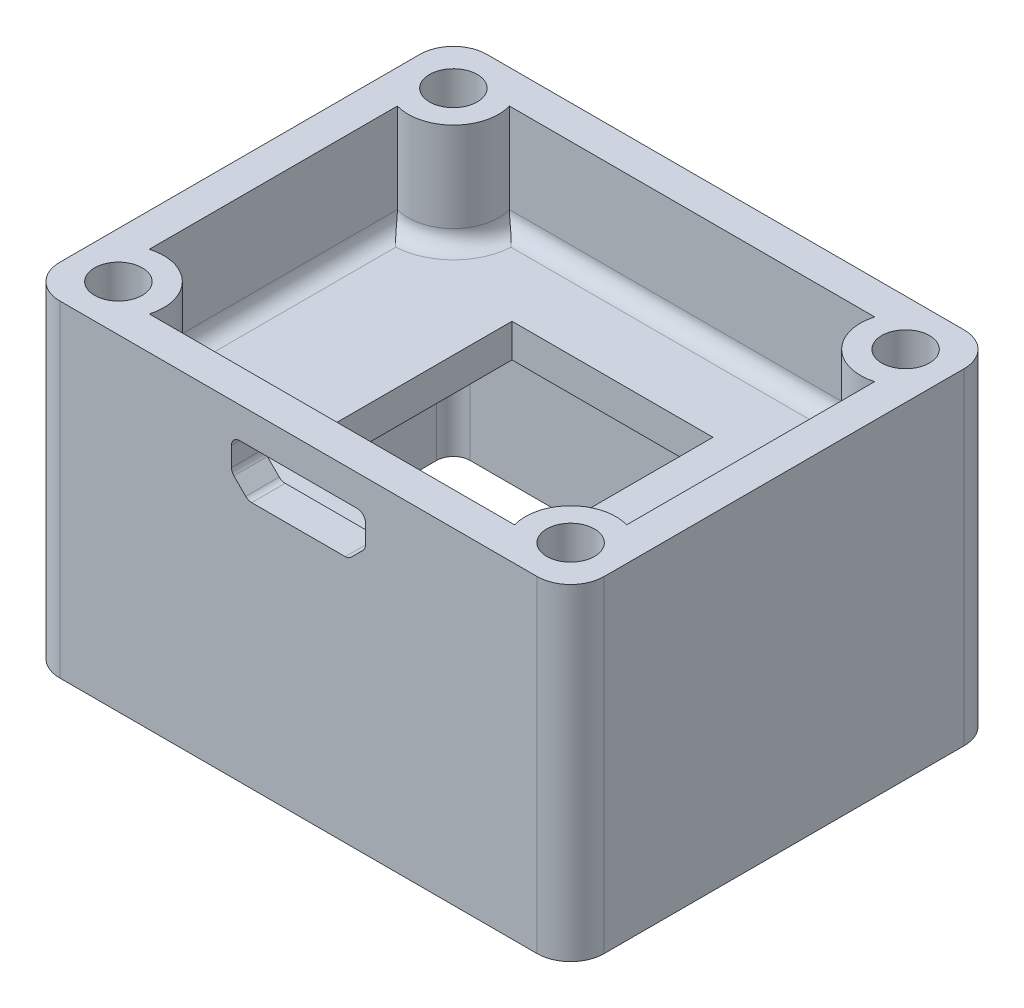
SolidWorks part; units mm, degrees
material "ABS"
ref_plane "Front" through (0, 0, 0) normal (0, 0, 1) x (1, 0, 0)
ref_plane "Top" through (0, 0, 0) normal (0, 1, 0) x (1, 0, 0)
ref_plane "Right" through (0, 0, 0) normal (1, 0, 0) x (0, 0, -1)
sketch "草图1" plane through (0, 0, 0) normal (0, 1, 0) x (1, 0, 0)
  line L0 (-14.25, 10.75) -> (-16.25, 10.75) construction
  line L5 (-14.25, 10.75) -> (14.25, 10.75)
  line L6 (-14.25, 10.75) -> (-14.25, -10.75)
  line L11 (-14.25, -10.75) -> (14.25, -10.75)
  line L12 (14.25, 10.75) -> (14.25, -10.75)
  line L13 (-14.25, 10.75) -> (14.25, -10.75) construction
  line L14 (-14.25, -10.75) -> (14.25, 10.75) construction
  line L15 (-16.25, 12.75) -> (16.25, 12.75)
  line L16 (-16.25, 12.75) -> (-16.25, -12.75)
  line L17 (-16.25, -12.75) -> (16.25, -12.75)
  line L18 (16.25, 12.75) -> (16.25, -12.75)
  line L19 (-16.25, 12.75) -> (16.25, -12.75) construction
  line L20 (-16.25, -12.75) -> (16.25, 12.75) construction
  line L21 (-14.25, 10.75) -> (-14.25, 12.75) construction
  point P0 (0, 0)
  point P6 (0, 0)
  dimension "D3" = 28.5
  dimension "D2" = 2
  dimension "D4" = 21.5
extrude "凸台-拉伸1" add sketch "草图1" along normal blind 13.2
sketch "草图2" plane through (0, 13.2, 0) normal (0, 1, 0) x (1, 0, 0)
  line L1 (-14.25, 10.75) -> (14.25, 10.75)
  line L2 (-14.25, 10.75) -> (-14.25, -10.75)
  line L3 (-14.25, -10.75) -> (14.25, -10.75)
  line L4 (14.25, 10.75) -> (14.25, -10.75)
  line L5 (-14.25, 10.75) -> (14.25, -10.75) construction
  line L6 (-14.25, -10.75) -> (14.25, 10.75) construction
  line L7 (-6, 6) -> (6, 6)
  line L8 (-6, 6) -> (-6, -6)
  line L9 (-6, -6) -> (6, -6)
  line L10 (6, 6) -> (6, -6)
  line L11 (-6, 6) -> (6, -6) construction
  line L12 (-6, -6) -> (6, 6) construction
  point P0 (0, 0)
  point P7 (0, 0)
  point P8 (0, 0)
  dimension "D1" = 12
extrude "凸台-拉伸2" add sketch "草图2" against normal blind 2
sketch "草图3" plane through (0, 13.2, 0) normal (0, 1, 0) x (1, 0, 0)
  line L0 (0, 0) -> (-16.25, 0) construction
  line L1 (-16.25, 12.75) -> (-16.25, -12.75) construction
  line L2 (-16.25, -12.75) -> (-16.25, 12.75)
  line L3 (-16.25, 12.75) -> (16.25, 12.75)
  line L4 (16.25, 12.75) -> (16.25, -0.0404)
  line L5 (16.25, -12.75) -> (16.25, 12.75) construction
  line L7 (14.25, 0.0137) -> (14.25, 10.75)
  line L8 (14.25, 10.75) -> (-14.25, 10.75)
  line L9 (-14.25, 10.75) -> (-14.25, -10.75)
  line L10 (14.25, -10.75) -> (-14.25, -10.75)
  line L11 (14.25, 0.0137) -> (14.25, -10.75)
  line L13 (16.25, -12.75) -> (16.25, -0.0404)
  line L14 (-16.25, -12.75) -> (16.25, -12.75)
  line L15 (14.25, 10.75) -> (-14.25, 10.75) construction
  line L16 (-14.25, 10.75) -> (-14.25, -10.75) construction
  line L17 (14.25, -10.75) -> (14.25, 10.75) construction
  point P17 (-14.25, 0)
extrude "凸台-拉伸3" add sketch "草图3" along normal blind 6.3
sketch "草图6" plane through (0, 19.5, 0) normal (0, 1, 0) x (1, 0, 0)
  line L0 (16.25, 0) -> (0, 0) construction
  line L2 (0, 0) -> (0, 12.75) construction
  line L4 (16.25, -12.75) -> (16.25, 12.75) construction
  line L5 (16.25, 12.75) -> (-16.25, 12.75) construction
  circle A0 centre (13.5, 10) radius 2.7
  circle A1 centre (13.5, -10) radius 2.7
  circle A2 centre (-13.5, -10) radius 2.7
  circle A3 centre (-13.5, 10) radius 2.7
  dimension "D1" = 5.4
  dimension "D2" = 27
  dimension "D3" = 20
extrude "凸台-拉伸4" add sketch "草图6" against normal up to next
sketch "草图7" plane through (0, 19.5, 0) normal (0, 1, 0) x (1, 0, 0)
  line L0 (0, 12.75) -> (0, 0) construction
  line L2 (0, 0) -> (16.25, 0) construction
  line L4 (16.25, 12.75) -> (-16.25, 12.75) construction
  line L5 (16.25, -12.75) -> (16.25, 12.75) construction
  circle A0 centre (13.5, 10) radius 1.425
  circle A1 centre (13.5, -10) radius 1.425
  circle A2 centre (-13.5, -10) radius 1.425
  circle A3 centre (-13.5, 10) radius 1.425
  dimension "D1" = 2.85
extrude "切除-拉伸3" cut sketch "草图7" against normal blind 5.5
sketch "草图10" plane through (0, 11.2, 0) normal (0, -1, 0) x (1, 0, 0)
  line L1 (-7.1, 7.1) -> (7.1, 7.1)
  line L2 (-7.1, 7.1) -> (-7.1, -7.1)
  line L3 (-7.1, -7.1) -> (7.1, -7.1)
  line L4 (7.1, 7.1) -> (7.1, -7.1)
  line L5 (-7.1, 7.1) -> (7.1, -7.1) construction
  line L6 (-7.1, -7.1) -> (7.1, 7.1) construction
  line L7 (-7.9, 7.9) -> (7.9, 7.9)
  line L8 (-7.9, 7.9) -> (-7.9, -7.9)
  line L9 (-7.9, -7.9) -> (7.9, -7.9)
  line L10 (7.9, 7.9) -> (7.9, -7.9)
  line L11 (-7.9, 7.9) -> (7.9, -7.9) construction
  line L12 (-7.9, -7.9) -> (7.9, 7.9) construction
  point P11 (0, 0)
  point P13 (0, 0)
  dimension "D1" = 14.2
  dimension "D2" = 0.8
extrude "凸台-拉伸5" add sketch "草图10" along normal blind 0.8 contours L10 L7 L8 L9 L1 L4 L3 L2
sketch "草图11" plane through (0, 0, 12.75) normal (0, 0, 1) x (1, 0, 0)
  line L0 (0, 0) -> (0, 19.5) construction
  line L1 (-4, 17.65) -> (4, 17.65)
  line L2 (4, 17.65) -> (4, 15.8)
  line L3 (4, 15.8) -> (3, 14.8)
  line L4 (3, 14.8) -> (-3, 14.8)
  line L5 (-4, 15.8) -> (-3, 14.8)
  line L6 (-4, 17.65) -> (-4, 15.8)
  line L7 (-16.25, 19.5) -> (16.25, 19.5) construction
  line L8 (-10.9063, 13.2) -> (10.9063, 13.2) construction
  point P7 (0, 14.8)
  point P9 (0, 17.65)
  dimension "D1" = 8
  dimension "D2" = 135
  dimension "D3" = 1
  dimension "D4" = 1.6
  dimension "D5" = 2.85
extrude "切除-拉伸5" cut sketch "草图11" against normal blind 3
fillet "圆角6" radius 0.5 6 edges at (4, 15.8, 11.75) (3, 14.8, 11.75) (-3, 14.8, 11.75) (-4, 15.8, 11.75) (-4, 17.65, 11.75) (4, 17.65, 11.75)
fillet "圆角3" radius 0.95 8 edges at (0, 13.2, -10.75) (11.5908, 13.2, -8.0908) (11.5908, 13.2, 8.0908) (0, 13.2, 10.75) (-11.5908, 13.2, 8.0908) (-14.25, 13.2, 0) (-11.5908, 13.2, -8.0908) (14.25, 13.2, 0)
fillet "圆角1" radius 2 4 edges at (16.25, 9.75, -12.75) (-16.25, 9.75, 12.75) (16.25, 9.75, 12.75) (-16.25, 9.75, -12.75)
fillet "圆角2" radius 1 4 edges at (14.25, 5.6, -10.75) (-14.25, 5.6, -10.75) (-14.25, 5.6, 10.75) (14.25, 5.6, 10.75)
